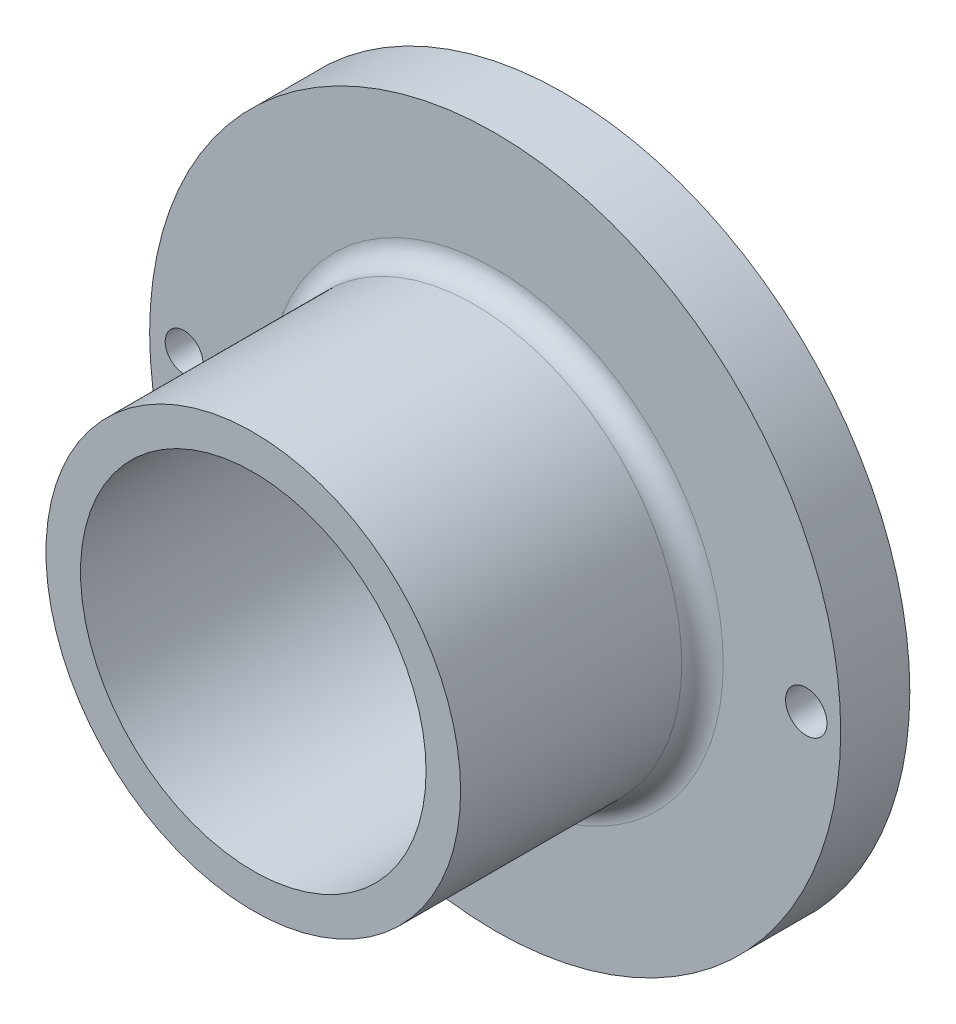
SolidWorks part; units mm, degrees
ref_plane "Front Plane" through (0, 0, 0) normal (0, 0, 1) x (1, 0, 0)
ref_plane "Top Plane" through (0, 0, 0) normal (0, 1, 0) x (1, 0, 0)
ref_plane "Right Plane" through (0, 0, 0) normal (1, 0, 0) x (0, 0, -1)
sketch "Sketch1" plane through (0, 0, 0) normal (0, 0, 1) x (1, 0, 0)
  circle A0 centre (0, 0) radius 50
  circle A1 centre (0, 0) radius 25
extrude "Boss-Extrude1" add sketch "Sketch1" along normal blind 10
sketch "Sketch2" plane through (0, 0, 0) normal (0, 0, 1) x (1, 0, 0)
  circle A0 centre (0, 0) radius 25
  circle A1 centre (0, 0) radius 30
extrude "Boss-Extrude2" add sketch "Sketch2" along normal blind 45
fillet "Fillet1" radius 3 1 edges at (30, 0, 10)
sketch "Sketch3" plane through (0, 0, 0) normal (0, 0, 1) x (1, 0, 0)
  line L0 (-52.8482, 0) -> (55.7134, 0) construction
  circle A1 centre (45.0165, 0) radius 3
  circle A2 centre (-45.0165, 0) radius 2.7289
  point P0 (0, 0)
extrude "Cut-Extrude1" cut sketch "Sketch3" along normal blind 50
